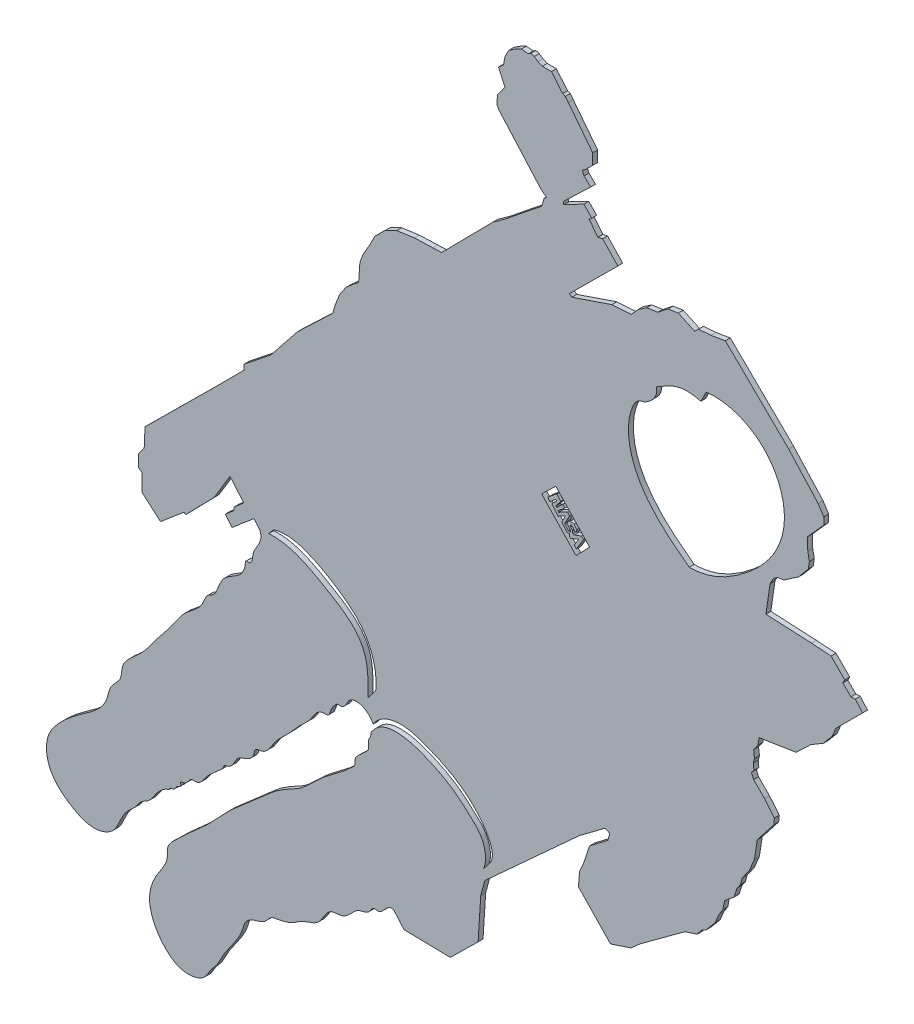
SolidWorks part; units mm, degrees
ref_plane "Front Plane" through (0, 0, 0) normal (0, 0, 1) x (1, 0, 0)
ref_plane "Top Plane" through (0, 0, 0) normal (0, 1, 0) x (1, 0, 0)
ref_plane "Right Plane" through (0, 0, 0) normal (1, 0, 0) x (0, 0, -1)
sketch "Sketch1" plane through (0, 0, 0) normal (0, 0, 1) x (1, 0, 0)
  line L0 (68.165, 169.3218) -> (381.3721, 169.3218) construction
  line L1 (78.8748, 82.5974) -> (77.9218, 83.7173)
  line L2 (77.9218, 83.7173) -> (73.4761, 79.9342)
  line L3 (73.4761, 79.9342) -> (72.0777, 81.5776)
  line L4 (72.0777, 81.5776) -> (73.8497, 83.0855)
  line L5 (73.8497, 83.0855) -> (73.8497, 83.7173)
  line L6 (73.8497, 83.7173) -> (75.8483, 85.418)
  line L7 (75.8483, 85.418) -> (73.049, 88.7076)
  line L8 (73.049, 88.7076) -> (69.8313, 83.4014)
  line L9 (69.8313, 83.4014) -> (68.2943, 81.8257)
  line L10 (68.2943, 81.8257) -> (64.0229, 77.4471)
  line L11 (64.0229, 77.4471) -> (63.7159, 77.7465)
  line L12 (63.7159, 77.7465) -> (58.9393, 73.6818)
  line L13 (58.9393, 73.6818) -> (55.1775, 76.9608)
  line L14 (55.1775, 76.9608) -> (55.1775, 80.4957)
  line L15 (55.1775, 80.4957) -> (54.4881, 80.9137)
  line L16 (54.4881, 80.9137) -> (54.4881, 83.4014)
  line L17 (54.4881, 83.4014) -> (55.6271, 84.9867)
  line L18 (55.6271, 84.9867) -> (55.7932, 88.8079)
  line L19 (55.7932, 88.8079) -> (69.3952, 102.2825)
  line L20 (69.3952, 102.2825) -> (75.8902, 108.8017)
  line L21 (75.8902, 108.8017) -> (75.939, 109.8997)
  line L22 (75.939, 109.8997) -> (81.3316, 114.1943)
  line L23 (81.3316, 114.1943) -> (86.7335, 120.9751)
  line L24 (86.7335, 120.9751) -> (93.8893, 127.7947)
  line L25 (93.8893, 127.7947) -> (94.4685, 129.7036)
  line L26 (94.4685, 129.7036) -> (95.4075, 132.0511)
  line L27 (95.4075, 132.0511) -> (96.6469, 133.76)
  line L28 (96.6469, 133.76) -> (98.2244, 135.1497)
  line L29 (98.2244, 135.1497) -> (99.1633, 135.8425)
  line L30 (99.1633, 135.8425) -> (99.4218, 139.5037)
  line L31 (99.4218, 139.5037) -> (100.0678, 141.2697)
  line L32 (100.0678, 141.2697) -> (101.3816, 143.531)
  line L33 (101.3816, 143.531) -> (102.4799, 145.663)
  line L34 (102.4799, 145.663) -> (104.6335, 147.7736)
  line L35 (104.6335, 147.7736) -> (106.8948, 148.8504)
  line L36 (106.8948, 148.8504) -> (110.4914, 149.3673)
  line L37 (110.4914, 149.3673) -> (114.2602, 149.4965)
  line L38 (114.2602, 149.4965) -> (116.0262, 149.5611)
  line L39 (116.0262, 149.5611) -> (126.4464, 160.1229)
  line L40 (126.4464, 160.1229) -> (129.026, 161.971)
  line L41 (129.026, 161.971) -> (134.0698, 166.0522)
  line L42 (134.0698, 166.0522) -> (136.3415, 167.8233)
  line L43 (136.3415, 167.8233) -> (136.842, 169.5174)
  line L44 (136.842, 169.5174) -> (137.3425, 169.9025)
  line L45 (137.3425, 169.9025) -> (136.226, 170.7495)
  line L46 (136.226, 170.7495) -> (127.717, 180.3751)
  line L47 (127.717, 180.3751) -> (127.2276, 181.243)
  line L48 (127.2276, 181.243) -> (127.3792, 182.9859)
  line L49 (127.3792, 182.9859) -> (128.8948, 185.032)
  line L50 (128.8948, 185.032) -> (127.5686, 187.9495)
  line L51 (127.5686, 187.9495) -> (128.5917, 188.8589)
  line L52 (128.5917, 188.8589) -> (128.8948, 190.4882)
  line L53 (128.8948, 190.4882) -> (129.6905, 191.9659)
  line L54 (129.6905, 191.9659) -> (131.1682, 192.951)
  line L55 (131.1682, 192.951) -> (132.2291, 193.4436)
  line L56 (132.2291, 193.4436) -> (133.6689, 193.3299)
  line L57 (133.6689, 193.3299) -> (134.1615, 193.6709)
  line L58 (134.1615, 193.6709) -> (134.8435, 193.4436)
  line L59 (134.8435, 193.4436) -> (135.6392, 192.9131)
  line L60 (135.6392, 192.9131) -> (136.4728, 192.5342)
  line L61 (136.4728, 192.5342) -> (138.3294, 192.5342)
  line L62 (138.3294, 192.5342) -> (140.6028, 189.8061)
  line L63 (140.6028, 189.8061) -> (141.1332, 189.5788)
  line L64 (141.1332, 189.5788) -> (141.7395, 188.821)
  line L65 (141.7395, 188.821) -> (146.7051, 182.4351)
  line L66 (146.7051, 182.4351) -> (146.7051, 180.2181)
  line L67 (146.7051, 180.2181) -> (145.0487, 178.5872)
  line L68 (145.0487, 178.5872) -> (144.5646, 178.3579)
  line L69 (144.5646, 178.3579) -> (144.9468, 177.4915)
  line L70 (144.9468, 177.4915) -> (146.2719, 176.1919)
  line L71 (146.2719, 176.1919) -> (140.8187, 170.9681)
  line L72 (140.8187, 170.9681) -> (140.8187, 170.382)
  line L73 (140.8187, 170.382) -> (144.9213, 172.5225)
  line L74 (144.9213, 172.5225) -> (146.5047, 170.8431)
  line L75 (146.5047, 170.8431) -> (145.9718, 170.373)
  line L76 (145.9718, 170.373) -> (147.7586, 168.116)
  line L77 (147.7586, 168.116) -> (148.7303, 168.3355)
  line L78 (148.7303, 168.3355) -> (151.8022, 165.0755)
  line L79 (151.8022, 165.0755) -> (141.9595, 155.2955)
  line L80 (141.9595, 155.2955) -> (142.4611, 154.9193)
  line L81 (142.4611, 154.9193) -> (150.5797, 157.6778)
  line L82 (150.5797, 157.6778) -> (154.5293, 157.9285)
  line L83 (154.5293, 157.9285) -> (155.9399, 159.4958)
  line L84 (155.9399, 159.4958) -> (157.6953, 160.687)
  line L85 (157.6953, 160.687) -> (159.9209, 161.0005)
  line L86 (159.9209, 161.0005) -> (162.0211, 162.6305)
  line L87 (162.0211, 162.6305) -> (164.0899, 162.9439)
  line L88 (164.0899, 162.9439) -> (167.4126, 161.408)
  line L89 (167.4126, 161.408) -> (168.1963, 162.1603)
  line L90 (168.1963, 162.1603) -> (170.7353, 162.3483)
  line L91 (170.7353, 162.3483) -> (173.6505, 162.8499)
  line L92 (173.6505, 162.8499) -> (186.4798, 150.267)
  line L93 (186.4798, 150.267) -> (192.471, 143.6501)
  line L94 (192.471, 143.6501) -> (193.626, 141.8696)
  line L95 (193.626, 141.8696) -> (193.626, 140.4019)
  line L96 (193.626, 140.4019) -> (190.3105, 136.7077)
  line L97 (190.3105, 136.7077) -> (190.3779, 134.2298)
  line L98 (190.3779, 134.2298) -> (190.6982, 132.5442)
  line L99 (190.6982, 132.5442) -> (190.4959, 131.1283)
  line L100 (190.4959, 131.1283) -> (188.49, 128.7347)
  line L101 (188.49, 128.7347) -> (185.4959, 126.7033)
  line L102 (185.4959, 126.7033) -> (184.2717, 126.5241)
  line L103 (184.2717, 126.5241) -> (183.4655, 125.9867)
  line L104 (183.4655, 125.9867) -> (182.719, 124.6729)
  line L105 (182.719, 124.6729) -> (181.883, 118.8803)
  line L106 (181.883, 118.8803) -> (191.1145, 118.4138)
  line L107 (191.1145, 118.4138) -> (195.1013, 118.1445)
  line L108 (195.1013, 118.1445) -> (197.9028, 115.343)
  line L109 (197.9028, 115.343) -> (197.4987, 114.6156)
  line L110 (197.4987, 114.6156) -> (199.1419, 112.9725)
  line L111 (199.1419, 112.9725) -> (200.0309, 113.0263)
  line L112 (200.0309, 113.0263) -> (201.5124, 111.3293)
  line L113 (201.5124, 111.3293) -> (196.0765, 105.9025)
  line L114 (196.0765, 105.9025) -> (195.3181, 104.1127)
  line L115 (195.3181, 104.1127) -> (193.5586, 102.0195)
  line L116 (193.5586, 102.0195) -> (191.0103, 100.5027)
  line L117 (191.0103, 100.5027) -> (188.007, 97.6511)
  line L118 (188.007, 97.6511) -> (180.4836, 96.4679)
  line L119 (180.4836, 96.4679) -> (180.2596, 95.0208)
  line L120 (180.2596, 95.0208) -> (179.3789, 93.8256)
  line L121 (179.3789, 93.8256) -> (179.5677, 92.3159)
  line L122 (179.5677, 92.3159) -> (179.316, 91.4352)
  line L123 (179.316, 91.4352) -> (179.4419, 90.1771)
  line L124 (179.4419, 90.1771) -> (178.9386, 89.611)
  line L125 (178.9386, 89.611) -> (179.3789, 88.5416)
  line L126 (179.3789, 88.5416) -> (181.5806, 86.3399)
  line L127 (181.5806, 86.3399) -> (183.5936, 83.8866)
  line L128 (183.5936, 83.8866) -> (183.4678, 82.6285)
  line L129 (183.4678, 82.6285) -> (180.1338, 78.3509)
  line L130 (180.1338, 78.3509) -> (179.5525, 74.6338)
  line L131 (179.5525, 74.6338) -> (178.529, 72.1482)
  line L132 (178.529, 72.1482) -> (177.0669, 70.1013)
  line L133 (177.0669, 70.1013) -> (176.7014, 68.7123)
  line L134 (176.7014, 68.7123) -> (176.0434, 67.8351)
  line L135 (176.0434, 67.8351) -> (175.3855, 65.8612)
  line L136 (175.3855, 65.8612) -> (173.4848, 64.326)
  line L137 (173.4848, 64.326) -> (173.1193, 62.4984)
  line L138 (173.1193, 62.4984) -> (172.3882, 61.4019)
  line L139 (172.3882, 61.4019) -> (171.5841, 59.5011)
  line L140 (171.5841, 59.5011) -> (169.7565, 57.308)
  line L141 (169.7565, 57.308) -> (168.8061, 56.7963)
  line L142 (168.8061, 56.7963) -> (167.9288, 55.6266)
  line L143 (167.9288, 55.6266) -> (165.4433, 54.8225)
  line L144 (165.4433, 54.8225) -> (156.3783, 48.17)
  line L145 (156.3783, 48.17) -> (154.4776, 46.4886)
  line L146 (154.4776, 46.4886) -> (150.3107, 45.0996)
  line L147 (150.3107, 45.0996) -> (143.8044, 51.8983)
  line L148 (143.8044, 51.8983) -> (144.0237, 54.6763)
  line L149 (144.0237, 54.6763) -> (144.8278, 56.5039)
  line L150 (144.8278, 56.5039) -> (146.0706, 60.2322)
  line L151 (146.0706, 60.2322) -> (149.7989, 63.0833)
  line L152 (149.7989, 63.0833) -> (150.1645, 64.4722)
  line L153 (150.1645, 64.4722) -> (149.2141, 64.9109)
  line L154 (149.2141, 64.9109) -> (143.9506, 60.9632)
  line L155 (143.9506, 60.9632) -> (124.7972, 43.4913)
  line L156 (124.7972, 43.4913) -> (123.9683, 40.4464)
  line L157 (123.9683, 40.4464) -> (123.4309, 32.0271)
  line L158 (123.4309, 32.0271) -> (117.7881, 26.4739)
  line L159 (117.7881, 26.4739) -> (108.3835, 26.653)
  line L160 (108.3835, 26.653) -> (106.3492, 29.0251)
  line L161 (168.6734, 149.7264) -> (169.7565, 151.886)
  line L162 (102.3221, 58.8322) -> (101.7055, 58.0547)
  line L163 (102.3736, 60.0454) -> (102.1456, 59.6958)
  line L164 (101.0741, 63.7582) -> (102.6388, 65.8276)
  line L165 (80.935, 82.5974) -> (81.9445, 83.7458)
  line L166 (139.2053, 120.0396) -> (146.0706, 112.7696)
  line L167 (146.0706, 112.7696) -> (143.3025, 109.8997)
  line L168 (143.3025, 109.8997) -> (136.3415, 117.271)
  line L169 (136.3415, 117.271) -> (139.2053, 120.0396)
  line L170 (139.198, 118.6644) -> (137.565, 117.2799)
  line L171 (137.565, 117.2799) -> (138.0165, 116.7474)
  line L172 (138.0165, 116.7474) -> (139.2053, 117.7553)
  line L173 (139.2053, 117.7553) -> (139.3895, 117.538)
  line L174 (139.3895, 117.538) -> (138.389, 116.5707)
  line L175 (138.389, 116.5707) -> (139.7094, 115.0133)
  line L176 (139.7094, 115.0133) -> (141.1332, 115.792)
  line L177 (141.1332, 115.792) -> (140.4213, 114.3113)
  line L178 (140.4213, 114.3113) -> (141.4608, 113.0853)
  line L179 (141.4608, 113.0853) -> (141.9595, 113.0853)
  line L180 (141.9595, 113.0853) -> (141.9595, 112.59)
  line L181 (141.9595, 112.59) -> (142.1921, 112.3511)
  line L182 (142.1921, 112.3511) -> (143.8517, 113.0526)
  line L183 (143.8517, 113.0526) -> (142.962, 111.5812)
  line L184 (142.962, 111.5812) -> (143.3897, 111.1021)
  line L185 (143.3897, 111.1021) -> (144.8269, 113.4974)
  line L186 (144.8269, 113.4974) -> (144.3992, 113.8909)
  line L187 (144.3992, 113.8909) -> (142.9791, 113.3776)
  line L188 (142.9791, 113.3776) -> (142.6712, 113.3948)
  line L189 (142.6712, 113.3948) -> (142.6027, 114.0107)
  line L190 (142.6027, 114.0107) -> (142.1921, 114.4213)
  line L191 (142.1921, 114.4213) -> (142.2605, 114.8148)
  line L192 (142.2605, 114.8148) -> (142.6369, 114.5924)
  line L193 (142.6369, 114.5924) -> (143.0989, 113.9765)
  line L194 (143.0989, 113.9765) -> (143.424, 114.062)
  line L195 (143.424, 114.062) -> (143.4753, 114.5411)
  line L196 (143.4753, 114.5411) -> (142.8765, 115.2426)
  line L197 (141.0287, 114.4213) -> (141.7473, 113.5145)
  line L198 (141.0287, 114.4213) -> (141.9868, 116.2178)
  line L199 (141.9868, 116.2178) -> (141.6104, 116.6968)
  line L200 (141.6104, 116.6968) -> (139.7797, 115.7558)
  line L201 (139.7797, 115.7558) -> (139.677, 115.9954)
  line L202 (139.677, 115.9954) -> (141.0287, 117.1075)
  line L203 (141.0287, 117.1075) -> (140.6352, 117.5523)
  line L204 (140.6352, 117.5523) -> (139.3349, 116.3718)
  line L205 (139.3349, 116.3718) -> (139.2664, 116.6455)
  line L206 (139.2664, 116.6455) -> (140.2074, 117.8774)
  line L207 (140.2074, 117.8774) -> (139.4375, 118.8184)
  line L208 (139.4375, 118.8184) -> (139.198, 118.6644)
  line L209 (141.7473, 113.5145) -> (142.1921, 113.4974)
  line L210 (142.1921, 113.4974) -> (142.1921, 113.7712)
  line L211 (142.1921, 113.7712) -> (141.4735, 114.5924)
  line L212 (141.4735, 114.5924) -> (141.6788, 115.1228)
  line L213 (141.6788, 115.1228) -> (142.1579, 115.3794)
  line L214 (142.1579, 115.3794) -> (142.8765, 115.2426)
  line L215 (124.5471, 45.4684) -> (125.9501, 47.2477)
  spline S0 degree 3 poles (102.1456, 59.6958) (101.8989, 60.1398) (100.9736, 61.3296) (99.0598, 62.2615) (97.1838, 61.5965) (96.6976, 60.341) (95.8692, 59.3465) (94.8191, 59.665) (94.2082, 58.9224) (93.5089, 58.1261) (93.2767, 56.4605) (91.5825, 56.7221) (90.3414, 55.7422) (89.34, 53.8077) (87.1877, 52.0999) (85.0453, 49.3382) (82.8097, 47.5225) (81.3231, 45.1932) (80.2338, 43.4707) (78.0184, 43.4957) (77.9606, 41.9794) (76.8987, 40.7637) (75.5202, 40.4826) (74.4279, 39.8075) (73.8919, 38.6068) (73.0521, 37.4854) (71.8131, 37.3547) (71.6483, 36.6469) (71.062, 36.0573) (70.1995, 35.3547) (69.1209, 34.4063) (67.8707, 33.1454) (66.896, 31.2398) (65.2615, 31.6675) (64.5017, 30.7741) (64.0236, 30.0253) (62.8428, 30.0514) (63.1668, 29.4122) (62.8035, 28.9065) (62.1861, 28.839) (61.9425, 28.1436) (61.4247, 27.8483) (60.8291, 27.8748) (60.7929, 27.4095) (60.2332, 27.3125) (59.3275, 26.7926) (57.9077, 25.4653) (56.9066, 23.3574) (54.7854, 22.5621) (54.0946, 21.0895) (52.5988, 19.8968) (50.9023, 17.923) (49.9394, 14.3317) (45.4455, 12.4142) (40.4109, 14.5209) (35.9131, 18.4074) (35.4143, 24.4603) (38.5341, 28.3593) (42.8273, 32.0106) (48.018, 34.9589) (48.5511, 39.9404) (51.188, 41.6946) (50.9255, 44.608) (52.8894, 46.7877) (55.6409, 48.9696) (58.2731, 52.9905) (61.3761, 56.455) (63.8961, 60.6559) (67.4409, 62.3788) (68.1676, 65.6068) (69.9447, 66.1709) (70.6941, 68.1533) (71.7846, 70.7675) (75.1101, 71.9009) (76.1327, 73.9867) (76.2015, 75.6229) (77.2406, 75.2536) (77.6688, 76.4957) (77.6989, 78.0734) (79.0706, 79.6279) (79.4777, 81.5132) (79.0804, 82.3558) (78.8748, 82.5974) knots 0.001138 0.001138 0.001138 0.001138 0.010414 0.026528 0.035541 0.04102 0.050263 0.054207 0.057844 0.065503 0.074323 0.080796 0.090933 0.100191 0.119012 0.138174 0.161942 0.168569 0.187358 0.194118 0.200813 0.209543 0.221102 0.224841 0.23161 0.243809 0.247524 0.251053 0.255094 0.26212 0.270698 0.280178 0.294452 0.301848 0.304184 0.314387 0.316835 0.320142 0.32275 0.326828 0.329634 0.334669 0.336729 0.338352 0.341313 0.345223 0.35733 0.37465 0.384239 0.394869 0.401685 0.4178 0.440048 0.463685 0.492886 0.532004 0.562827 0.588598 0.616138 0.664707 0.681808 0.698844 0.714081 0.727881 0.748107 0.776432 0.811302 0.830325 0.861682 0.875475 0.881643 0.892015 0.910319 0.930006 0.948075 0.950228 0.954689 0.960582 0.968644 0.983684 0.994779 1 1 1 1
  spline S1 degree 3 poles (101.7055, 58.0547) (101.688, 57.7913) (101.6341, 57.1528) (100.8922, 56.1866) (101.5059, 54.7468) (100.4604, 54.0226) (99.6084, 52.9881) (98.214, 52.1406) (98.552, 50.5247) (97.7607, 49.912) (95.7038, 47.8622) (91.4535, 45.3358) (88.3534, 41.4637) (84.9204, 39.6522) (82.3028, 38.2134) (78.1397, 34.1499) (73.4908, 30.7391) (68.2985, 24.6529) (63.8394, 21.2915) (60.0952, 17.3508) (60.4565, 15.2115) (59.6431, 13.2902) (57.7339, 10.7772) (55.8108, 5.6469) (58.6008, -0.1103) (63.2599, -3.6384) (67.8932, -2.7538) (69.0031, -0.0022) (70.4013, 1.2822) (71.2382, 3.1685) (73.1026, 6.1632) (75.3453, 8.8376) (76.0677, 12.1472) (77.9215, 13.2633) (80.2072, 13.5626) (81.146, 15.3745) (83.4048, 15.7608) (85.4591, 16.1531) (87.8924, 18.2057) (91.4942, 18.4993) (92.652, 22.7624) (95.3767, 22.564) (97.3802, 23.5332) (98.6305, 25.709) (101.2677, 25.7) (101.9212, 27.5586) (104.2858, 26.8483) (104.7594, 29.6503) (106.3492, 29.0251) knots 0.011329 0.011329 0.011329 0.011329 0.016894 0.02484 0.035496 0.043517 0.048499 0.065058 0.072122 0.079292 0.084288 0.135047 0.182467 0.186965 0.217657 0.245611 0.310319 0.34027 0.414271 0.435624 0.444984 0.458336 0.478494 0.512903 0.568691 0.599771 0.633985 0.648412 0.660541 0.673774 0.691789 0.735933 0.746509 0.761277 0.778182 0.7937 0.798299 0.82603 0.836865 0.865171 0.894835 0.908373 0.917841 0.94149 0.956069 0.966939 0.973608 1 1 1 1
  spline S2 degree 3 poles (169.7565, 151.886) (173.7599, 152.3627) (180.3525, 150.1959) (185.2786, 142.8074) (186.0641, 136.0729) (183.4337, 129.3509) (177.0541, 122.8854) (170.6289, 119.3343) (166.3077, 119.3567) knots 0 0 0 0 0.229405 0.35846 0.48826 0.600167 0.758427 1 1 1 1
  spline S3 degree 3 poles (166.3077, 119.3567) (162.6722, 122.0106) (157.449, 126.224) (153.775, 134.499) (153.7809, 140.3112) (155.675, 143.6631) (157.0453, 143.8092) knots 0 0 0 0 0.454386 0.635638 0.885915 1 1 1 1
  spline S4 degree 3 poles (157.0453, 143.8092) (158.468, 144.4243) (160.0787, 146.0214) (159.6065, 147.7351) knots 0 0 0 0 1 1 1 1
  spline S5 degree 3 poles (159.6065, 147.7351) (161.3113, 148.7904) (164.3285, 150.6033) (167.5879, 149.9575) (168.6734, 149.7264) knots 0 0 0 0 0.648468 1 1 1 1
  spline S6 degree 3 poles (80.935, 82.5974) (85.464, 82.8742) (91.2468, 79.5797) (97.8104, 75.5268) (101.3172, 70.506) (101.0593, 66.2985) (101.0741, 63.7582) knots 0 0 0 0 0.424643 0.625216 0.742802 1 1 1 1
  spline S7 degree 3 poles (81.9445, 83.7458) (84.5124, 84.5984) (89.3869, 83.2301) (95.3408, 79.7715) (101.4107, 74.8219) (102.9983, 69.1388) (102.6388, 65.8276) knots 0 0 0 0 0.252253 0.472596 0.674626 1 1 1 1
  spline S8 degree 3 poles (102.3736, 60.0454) (103.7722, 61.9462) (107.7985, 63.0015) (113.4677, 61.1283) (118.6079, 58.8086) (122.895, 55.3908) (125.6986, 51.5826) (126.7367, 48.7293) (125.9501, 47.2477) knots 0 0 0 0 0.209908 0.351243 0.554016 0.737878 0.855089 1 1 1 1
  spline S9 degree 3 poles (102.3221, 58.8322) (103.7384, 60.5153) (108.0182, 61.0356) (113.3857, 59.0736) (117.9416, 56.7501) (121.3774, 53.8158) (124.8565, 50.592) (125.1859, 47.0501) (124.5471, 45.4684) knots 0 0 0 0 0.195273 0.392515 0.551632 0.689958 0.834125 1 1 1 1
  point P226 (159.6489, 147.7736)
  point P299 (139.198, 118.6313)
  point P334 (0, 0)
  point P377 (190.158, 136.8916)
  point P397 (0, 0)
extrude "Boss-Extrude1" add sketch "Sketch1" along normal blind 1 contours S1 L160 L159 L158 L157 L156 L155 L154 L153 L152 L151 L150 L149 L148 L147 L146 L145 L144 L143 L142 L141 L140 L139 L138 L137 L136 L135 L134 L133 L132 L131 L130 L129 L128 L127 L126 L125 L124 L123 L122 L121 L120 L119 L118 L117 L116 L115 L114 L113 L112 L111 L110 L109 L108 L107 L106 L105 L104 L103 L102 L101 L100 L99 L98 L97 L96 L95 L94 L93 L92 L91 L90 L89 L88 L87 L86 L85 L84 L83 L82 L81 L80 L79 L78 L77 L76 L75 L74 L73 L72 L71 L70 L69 L68 L67 L66 L65 L64 L63 L62 L61 L60 L59 L58 L57 L56 L55 L54 L53 L52 L51 L50 L49 L48 L47 L46 L45 L44 L43 L42 L41 L40 L39 L38 L37 L36 L35 L34 L33 L32 L31 L30 L29 L28 L27 L26 L25 L24 L23 L22 L21 L20 L19 L18 L17 L16 L15 L14 L13 L12 L11 L10 L9 L8 L7 L6 L5 L4 L3 L2 L1 S0 L163 S8 L215 S9 L162 | S6 L164 S7 L165 | S3 S4 S5 L161 S2 | L168 L169 L166 L167 | L176 L177 L178 L179 L180 L181 L182 L183 L184 L185 L186 L187 L188 L189 L190 L191 L192 L193 L194 L195 L196 L214 L213 L212 L211 L210 L209 L197 L198 L199 L200 L201 L202 L203 L204 L205 L206 L207 L208 L170 L171 L172 L173 L174 L175
